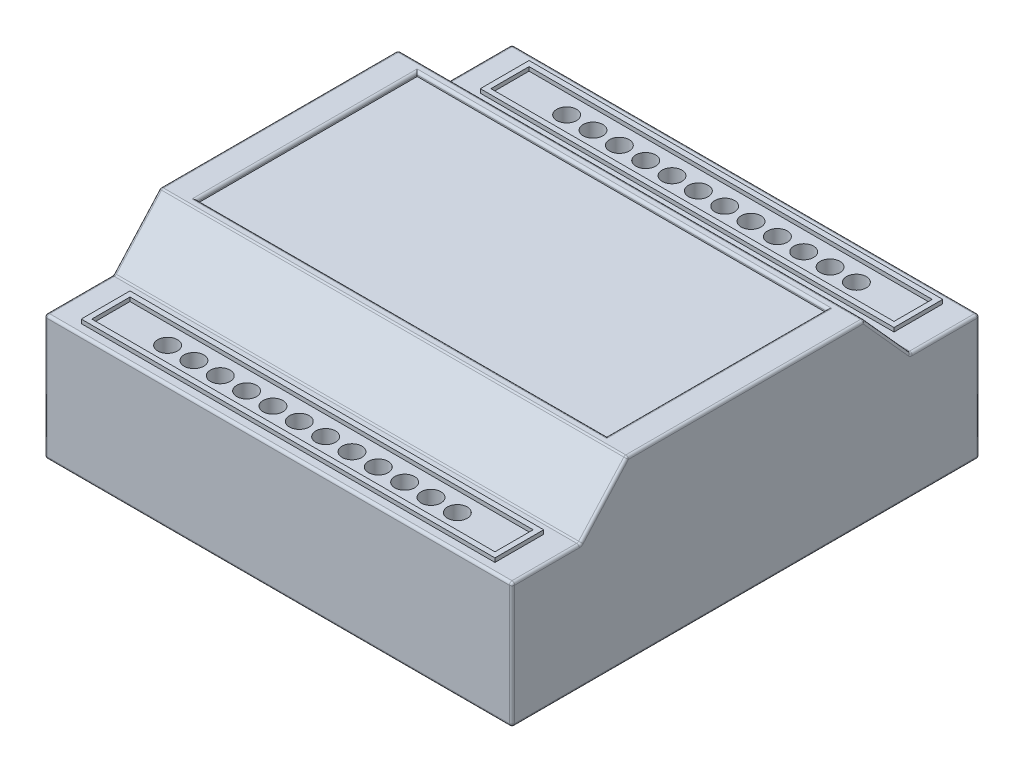
SolidWorks part; units mm, degrees
ref_plane "Front Plane" through (0, 0, 0) normal (0, 0, 1) x (1, 0, 0)
ref_plane "Top Plane" through (0, 0, 0) normal (0, 1, 0) x (1, 0, 0)
ref_plane "Right Plane" through (0, 0, 0) normal (1, 0, 0) x (0, 0, -1)
sketch "Sketch1" plane through (0, 0, 0) normal (0, 1, 0) x (1, 0, 0)
  line L1 (-45.085, -45.085) -> (45.085, -45.085)
  line L2 (-45.085, -45.085) -> (-45.085, 45.085)
  line L3 (-45.085, 45.085) -> (45.085, 45.085)
  line L4 (45.085, -45.085) -> (45.085, 45.085)
  line L5 (-45.085, -45.085) -> (45.085, 45.085) construction
  line L6 (-45.085, 45.085) -> (45.085, -45.085) construction
  point P0 (0, 0)
  dimension "D1" = 90.17
  dimension "D2" = 90.17
extrude "Boss-Extrude1" add sketch "Sketch1" along normal blind 34.163
sketch "Sketch2" plane through (45.085, 0, 0) normal (1, 0, 0) x (0, 0, -1)
  line L0 (-45.085, 24.13) -> (-45.085, 34.163)
  line L1 (-45.085, 34.163) -> (-45.085, 0) construction
  line L2 (-45.085, 34.163) -> (-22.86, 34.163)
  line L3 (-45.085, 34.163) -> (45.085, 34.163) construction
  line L4 (-22.86, 34.163) -> (-31.877, 24.13)
  line L5 (-31.877, 24.13) -> (-45.085, 24.13)
  line L6 (45.085, 24.13) -> (45.085, 34.163)
  line L7 (45.085, 34.163) -> (45.085, 0) construction
  line L8 (45.085, 34.163) -> (22.86, 34.163)
  line L9 (22.86, 34.163) -> (31.877, 24.13)
  line L10 (31.877, 24.13) -> (45.085, 24.13)
  point P14 (36.1972, 23.3109)
  point P17 (-35.9519, 23.5472)
  point P19 (22.86, 34.163)
  point P20 (31.3314, 25.4)
  point P21 (0, 0)
  dimension "D1" = 13.208
  dimension "D2" = 24.13
  dimension "D3" = 45.72
extrude "Cut-Extrude1" cut sketch "Sketch2" against normal through all
sketch "Sketch3" plane through (0, 34.163, 0) normal (0, 1, 0) x (1, 0, 0)
  line L1 (-39.497, -21.209) -> (39.497, -21.209)
  line L2 (-39.497, -21.209) -> (-39.497, 21.209)
  line L3 (-39.497, 21.209) -> (39.497, 21.209)
  line L4 (39.497, -21.209) -> (39.497, 21.209)
  line L5 (-39.497, -21.209) -> (39.497, 21.209) construction
  line L6 (-39.497, 21.209) -> (39.497, -21.209) construction
  point P0 (0, 0)
  dimension "D1" = 42.418
  dimension "D2" = 78.994
extrude "Cut-Extrude2" cut sketch "Sketch3" against normal blind 0.762
sketch "Sketch4" plane through (0, 24.13, 0) normal (0, 1, 0) x (1, 0, 0)
  line L0 (45.085, 31.877) -> (45.085, 45.085) construction
  line L1 (39.8907, 33.782) -> (-39.8907, 33.782)
  line L2 (39.8907, 33.782) -> (39.8907, 43.18)
  line L3 (39.8907, 43.18) -> (-39.8907, 43.18)
  line L4 (-39.8907, 33.782) -> (-39.8907, 43.18)
  line L5 (39.8907, 33.782) -> (-39.8907, 43.18) construction
  line L6 (39.8907, 43.18) -> (-39.8907, 33.782) construction
  line L7 (-38.8747, 34.798) -> (-38.8747, 42.164)
  line L8 (38.8747, 42.164) -> (-38.8747, 42.164)
  line L9 (38.8747, 34.798) -> (38.8747, 42.164)
  line L10 (38.8747, 34.798) -> (-38.8747, 34.798)
  point P0 (0, 38.481)
  point P5 (0, 0)
  point P8 (45.085, 38.481)
  point P9 (0, 0)
  dimension "D1" = 9.398
  dimension "D2" = 79.7814
  dimension "D3" = 1.016
extrude "Boss-Extrude2" add sketch "Sketch4" along normal blind 0.762
sketch "Sketch5" plane through (0, 24.13, 0) normal (0, 1, 0) x (1, 0, 0)
  line L0 (-45.085, 38.481) -> (45.085, 38.481) construction
  line L1 (45.085, 31.877) -> (45.085, 45.085) construction
  line L2 (0, 45.085) -> (0, 31.877) construction
  line L3 (-45.085, 45.085) -> (45.085, 45.085) construction
  line L4 (-45.085, 31.877) -> (45.085, 31.877) construction
  circle A0 centre (-2.54, 38.481) radius 1.905
  circle A1 centre (-7.62, 38.481) radius 1.905
  circle A2 centre (-12.7, 38.481) radius 1.905
  circle A3 centre (-17.78, 38.481) radius 1.905
  circle A4 centre (-22.86, 38.481) radius 1.905
  circle A5 centre (-27.94, 38.481) radius 1.905
  circle A6 centre (27.94, 38.481) radius 1.905
  circle A7 centre (22.86, 38.481) radius 1.905
  circle A8 centre (17.78, 38.481) radius 1.905
  circle A9 centre (12.7, 38.481) radius 1.905
  circle A10 centre (7.62, 38.481) radius 1.905
  circle A11 centre (2.54, 38.481) radius 1.905
  point P2 (0, 38.481)
  point P6 (45.085, 38.481)
  point P37 (-13.4379, 38.481)
  dimension "D1" = 3.81
  dimension "D2" = 0.635
  dimension "D4" = 1.27
  dimension "D3" = 6
extrude "Cut-Extrude3" cut sketch "Sketch5" against normal blind 5.08
mirror "Mirror1" about plane through (0, 0, 0) normal (0, 0, 1) of "Cut-Extrude3", "Boss-Extrude2"
fillet "Fillet1" radius 0.508 28 edges at (0, 34.163, -22.86) (45.085, 34.163, 0) (0, 34.163, 22.86) (-45.085, 34.163, 0) (0, 0, -45.085) (0, 24.13, -45.085) (0, 24.13, -31.877) (45.085, 29.1465, -27.3685) (45.085, 24.13, -38.481) (45.085, 12.065, -45.085) (45.085, 0, 0) (45.085, 12.065, 45.085) (-45.085, 12.065, -45.085) (-45.085, 24.13, -38.481) (-45.085, 29.1465, -27.3685) (45.085, 29.1465, 27.3685) (45.085, 24.13, 38.481) (0, 0, 45.085) (-45.085, 0, 0) (-45.085, 12.065, 45.085) (0, 24.13, 45.085) (0, 24.13, 31.877) (-45.085, 24.13, 38.481) (-45.085, 29.1465, 27.3685) (39.497, 34.163, 0) (0, 34.163, 21.209) (-39.497, 34.163, 0) (0, 34.163, -21.209)
